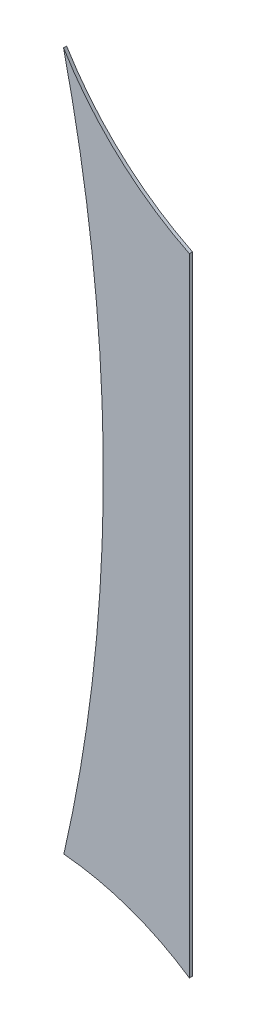
SolidWorks part; units mm, degrees
ref_plane "Alzado" through (0, 0, 0) normal (0, 0, 1) x (1, 0, 0)
ref_plane "Planta" through (0, 0, 0) normal (0, 1, 0) x (1, 0, 0)
ref_plane "Vista lateral" through (0, 0, 0) normal (1, 0, 0) x (0, 0, -1)
sketch "Model" plane through (0, 0, 0) normal (0, 0, 1) x (1, 0, 0)
  line L0 (21.1279, -7.6633) -> (21.126, 12.5397)
  arc A0 (21.1279, -7.6633) -> (17.081, -6.2289) centre (16.3398, -14.7461) ccw
  arc A1 (17.0736, 16.2544) -> (21.126, 12.5397) centre (25.5585, 21.443) ccw
  arc A2 (17.0844, -6.2292) -> (17.0736, 16.2544) centre (-31.7734, 4.989) ccw
extrude "Saliente-Extruir1" add sketch "Model" along normal blind 0.1 contours A2 A0 L0 A1
